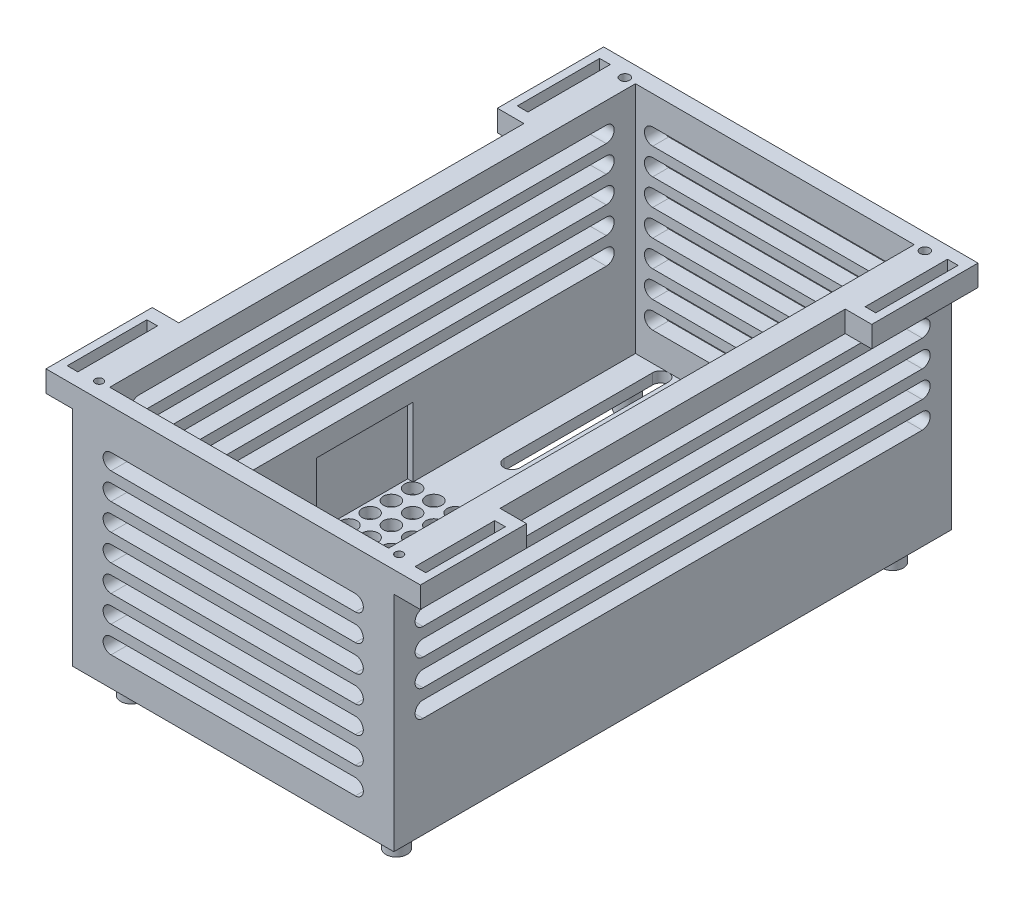
SolidWorks part; units mm, degrees
ref_plane "Front Plane" through (0, 0, 0) normal (0, 0, 1) x (1, 0, 0)
ref_plane "Top Plane" through (0, 0, 0) normal (0, 1, 0) x (1, 0, 0)
ref_plane "Right Plane" through (0, 0, 0) normal (1, 0, 0) x (0, 0, -1)
sketch "Sketch2" plane through (0, 0, 0) normal (0, 1, 0) x (1, 0, 0)
  line L1 (-30.25, 52.5) -> (30.25, 52.5)
  line L2 (-30.25, 52.5) -> (-30.25, -52.5)
  line L3 (-30.25, -52.5) -> (30.25, -52.5)
  line L4 (30.25, 52.5) -> (30.25, -52.5)
  line L5 (-30.25, 52.5) -> (30.25, -52.5) construction
  line L6 (-30.25, -52.5) -> (30.25, 52.5) construction
  point P0 (0, 0)
  dimension "D1" = 60.5
  dimension "D2" = 105
sketch "Sketch3" plane through (0, 0, 0) normal (0, 1, 0) x (1, 0, 0)
  line L0 (-30.25, -52.5) -> (30.25, -52.5) construction
  line L1 (30.25, 52.5) -> (26.25, 52.5)
  line L2 (30.25, 52.5) -> (30.25, -52.5)
  line L3 (30.25, -52.5) -> (26.25, -52.5)
  line L4 (26.25, 52.5) -> (26.25, -52.5)
  line L5 (0, 52.5) -> (0, -52.5) construction
  line L6 (-30.25, 52.5) -> (30.25, 52.5) construction
  line L7 (-30.25, -52.5) -> (-26.25, -52.5)
  line L8 (-26.25, 52.5) -> (-26.25, -52.5)
  line L9 (-30.25, 52.5) -> (-26.25, 52.5)
  line L10 (-30.25, 52.5) -> (-30.25, -52.5)
  line L12 (-30.25, 52.5) -> (30.25, 52.5)
  line L13 (-30.25, 52.5) -> (-30.25, 49.5)
  line L14 (-30.25, 49.5) -> (30.25, 49.5)
  line L15 (30.25, 52.5) -> (30.25, 49.5)
  dimension "D1" = 4
extrude "Boss-Extrude1" add sketch "Sketch3" along normal blind 46 contours L14 L10 L7 L8 | L5 L12 L8 L14 | L12 L5 L14 L4 | L14 L4 L3 L2 | L4 L14 L2 L1 | L10 L14 L8 L9
sketch "Sketch4" plane through (0, 0, 0) normal (0, 1, 0) x (1, 0, 0)
  line L1 (30.25, 52.5) -> (-30.25, 52.5)
  line L2 (30.25, 52.5) -> (30.25, -52.5)
  line L3 (30.25, -52.5) -> (-30.25, -52.5)
  line L4 (-30.25, 52.5) -> (-30.25, -52.5)
extrude "Boss-Extrude2" add sketch "Sketch4" along normal blind 2
sketch "Sketch5" plane through (0, 0, 0) normal (0, 1, 0) x (1, 0, 0)
  line L0 (0, -52.3325) -> (0, 52.2291) construction
  line L1 (30.25, -52.5) -> (30.25, -31.5) construction
  line L2 (30.25, 52.5) -> (30.25, -52.5) construction
  line L3 (30.25, -31.5) -> (-30.25, -31.5) construction
  line L4 (-30.25, 52.5) -> (-30.25, -52.5) construction
  line L5 (30.25, -28.023) -> (27.25, -28.023) construction
  line L7 (27.25, -31.5) -> (-13.75, -31.5)
  line L8 (27.25, -31.5) -> (27.25, 10.5)
  line L9 (27.25, 10.5) -> (-13.75, 10.5)
  line L10 (-13.75, -31.5) -> (-13.75, 10.5)
extrude "Cut-Extrude1" cut sketch "Sketch5" along normal blind 15
sketch "Sketch6" plane through (0, 0, 0) normal (0, 1, 0) x (1, 0, 0)
  circle A0 centre (-17.2261, -1.4891) radius 1.5
  circle A1 centre (-17.2261, -5.4891) radius 1.5
  circle A2 centre (-17.2261, -9.4891) radius 1.5
  circle A3 centre (-17.2261, 2.5109) radius 1.5
  circle A4 centre (-17.2261, 6.5109) radius 1.5
  circle A5 centre (-21.2261, -9.4891) radius 1.5
  circle A6 centre (-21.2261, -5.4891) radius 1.5
  circle A7 centre (-21.2261, -1.4891) radius 1.5
  circle A8 centre (-21.2261, 2.5109) radius 1.5
  circle A9 centre (-21.2261, 6.5109) radius 1.5
  circle A10 centre (-25.2261, -9.4891) radius 1.5
  circle A11 centre (-25.2261, -5.4891) radius 1.5
  circle A12 centre (-25.2261, -1.4891) radius 1.5
  circle A13 centre (-25.2261, 2.5109) radius 1.5
  circle A14 centre (-25.2261, 6.5109) radius 1.5
  dimension "D1" = 3
  dimension "D2" = 3
  dimension "D3" = 3
extrude "Cut-Extrude4" cut sketch "Sketch6" along normal blind 15
sketch "Sketch15" plane through (0, 0, 0) normal (0, -1, 0) x (1, 0, 0)
  line L0 (25.4448, -10.5) -> (25.4448, -15.5) construction
  line L1 (27.25, -10.5) -> (-13.75, -10.5) construction
  line L2 (25.4448, -15.5) -> (-17.3619, -15.5) construction
  line L3 (30.25, -15.5) -> (30.25, -52.5) construction
  line L4 (30.25, -52.5) -> (30.25, 52.5) construction
  line L5 (30.25, -52.5) -> (-30.25, -52.5) construction
  line L6 (0, -20) -> (0, -48) construction
  line L7 (5, -20) -> (5, -48) construction
  line L8 (1.5, -20) -> (1.5, -48)
  line L9 (-1.5, -20) -> (-1.5, -48)
  line L10 (6.5, -20) -> (6.5, -48)
  line L11 (3.5, -20) -> (3.5, -48)
  line L12 (10, -20) -> (10, -48) construction
  line L13 (11.5, -20) -> (11.5, -48)
  line L14 (8.5, -20) -> (8.5, -48)
  line L15 (15, -20) -> (15, -48) construction
  line L16 (16.5, -20) -> (16.5, -48)
  line L17 (13.5, -20) -> (13.5, -48)
  line L18 (20, -20) -> (20, -48) construction
  line L19 (21.5, -20) -> (21.5, -48)
  line L20 (18.5, -20) -> (18.5, -48)
  line L21 (-5, -20) -> (-5, -48) construction
  line L22 (-3.5, -20) -> (-3.5, -48)
  line L23 (-6.5, -20) -> (-6.5, -48)
  line L24 (-10, -20) -> (-10, -48) construction
  line L25 (-8.5, -20) -> (-8.5, -48)
  line L26 (-11.5, -20) -> (-11.5, -48)
  line L27 (-15, -20) -> (-15, -48) construction
  line L28 (-13.5, -20) -> (-13.5, -48)
  line L29 (-16.5, -20) -> (-16.5, -48)
  line L30 (-20, -20) -> (-20, -48) construction
  line L31 (-18.5, -20) -> (-18.5, -48)
  line L32 (-21.5, -20) -> (-21.5, -48)
  arc A0 (1.5, -20) -> (-1.5, -20) centre (0, -20) ccw
  arc A1 (-1.5, -48) -> (1.5, -48) centre (0, -48) ccw
  arc A2 (6.5, -20) -> (3.5, -20) centre (5, -20) ccw
  arc A3 (3.5, -48) -> (6.5, -48) centre (5, -48) ccw
  arc A4 (11.5, -20) -> (8.5, -20) centre (10, -20) ccw
  arc A5 (8.5, -48) -> (11.5, -48) centre (10, -48) ccw
  arc A6 (16.5, -20) -> (13.5, -20) centre (15, -20) ccw
  arc A7 (13.5, -48) -> (16.5, -48) centre (15, -48) ccw
  arc A8 (21.5, -20) -> (18.5, -20) centre (20, -20) ccw
  arc A9 (18.5, -48) -> (21.5, -48) centre (20, -48) ccw
  arc A10 (-3.5, -20) -> (-6.5, -20) centre (-5, -20) ccw
  arc A11 (-6.5, -48) -> (-3.5, -48) centre (-5, -48) ccw
  arc A12 (-8.5, -20) -> (-11.5, -20) centre (-10, -20) ccw
  arc A13 (-11.5, -48) -> (-8.5, -48) centre (-10, -48) ccw
  arc A14 (-13.5, -20) -> (-16.5, -20) centre (-15, -20) ccw
  arc A15 (-16.5, -48) -> (-13.5, -48) centre (-15, -48) ccw
  arc A16 (-18.5, -20) -> (-21.5, -20) centre (-20, -20) ccw
  arc A17 (-21.5, -48) -> (-18.5, -48) centre (-20, -48) ccw
  point P17 (0, -34)
  point P23 (5, -34)
  point P30 (10, -34)
  point P37 (15, -34)
  point P44 (20, -34)
  point P51 (-5, -34)
  point P58 (-10, -34)
  point P65 (-15, -34)
  point P72 (-20, -34)
  dimension "D1" = 5
  dimension "D2" = 5
extrude "Cut-Extrude15" cut sketch "Sketch15" against normal blind 15
sketch "Sketch16" plane through (-30.25, 0, 0) normal (-1, 0, 0) x (0, 0, 1)
  line L0 (-44, 40.488) -> (44, 40.488) construction
  line L1 (-44, 35.488) -> (44, 35.488) construction
  line L2 (-44, 41.988) -> (44, 41.988)
  line L3 (-44, 38.988) -> (44, 38.988)
  line L4 (-44, 36.988) -> (44, 36.988)
  line L5 (-44, 33.988) -> (44, 33.988)
  line L6 (-44, 30.488) -> (44, 30.488) construction
  line L7 (-44, 31.988) -> (44, 31.988)
  line L8 (-44, 28.988) -> (44, 28.988)
  line L9 (-44, 25.488) -> (44, 25.488) construction
  line L10 (-44, 26.988) -> (44, 26.988)
  line L11 (-44, 23.988) -> (44, 23.988)
  line L12 (-44, 20.488) -> (44, 20.488) construction
  line L13 (-44, 21.988) -> (44, 21.988)
  line L14 (-44, 18.988) -> (44, 18.988)
  arc A0 (-44, 41.988) -> (-44, 38.988) centre (-44, 40.488) ccw
  arc A1 (44, 38.988) -> (44, 41.988) centre (44, 40.488) ccw
  arc A2 (-44, 36.988) -> (-44, 33.988) centre (-44, 35.488) ccw
  arc A3 (44, 33.988) -> (44, 36.988) centre (44, 35.488) ccw
  arc A4 (-44, 31.988) -> (-44, 28.988) centre (-44, 30.488) ccw
  arc A5 (44, 28.988) -> (44, 31.988) centre (44, 30.488) ccw
  arc A6 (-44, 26.988) -> (-44, 23.988) centre (-44, 25.488) ccw
  arc A7 (44, 23.988) -> (44, 26.988) centre (44, 25.488) ccw
  arc A8 (-44, 21.988) -> (-44, 18.988) centre (-44, 20.488) ccw
  arc A9 (44, 18.988) -> (44, 21.988) centre (44, 20.488) ccw
  point P4 (0, 40.488)
  point P11 (0, 35.488)
  point P18 (0, 30.488)
  point P25 (0, 25.488)
  point P32 (0, 20.488)
  dimension "D1" = 5
extrude "Cut-Extrude16" cut sketch "Sketch16" against normal blind 15
sketch "Sketch20" plane through (30.25, 0, 0) normal (1, 0, 0) x (0, 0, -1)
  line L0 (0, 46) -> (0, 40.5) construction
  line L1 (52.5, 46) -> (-52.5, 46) construction
  line L2 (-47, 40.5) -> (47, 40.5) construction
  line L3 (-47, 35.5) -> (47, 35.5) construction
  line L4 (-47, 42) -> (47, 42)
  line L5 (-47, 39) -> (47, 39)
  line L6 (-47, 37) -> (47, 37)
  line L7 (-47, 34) -> (47, 34)
  line L8 (-47, 30.5) -> (47, 30.5) construction
  line L9 (-47, 32) -> (47, 32)
  line L10 (-47, 29) -> (47, 29)
  line L11 (-47, 25.5) -> (47, 25.5) construction
  line L12 (-47, 27) -> (47, 27)
  line L13 (-47, 24) -> (47, 24)
  line L14 (-47, 20.5) -> (47, 20.5) construction
  line L15 (-47, 22) -> (47, 22)
  line L16 (-47, 19) -> (47, 19)
  arc A0 (-47, 42) -> (-47, 39) centre (-47, 40.5) ccw
  arc A1 (47, 39) -> (47, 42) centre (47, 40.5) ccw
  arc A2 (-47, 37) -> (-47, 34) centre (-47, 35.5) ccw
  arc A3 (47, 34) -> (47, 37) centre (47, 35.5) ccw
  arc A4 (-47, 32) -> (-47, 29) centre (-47, 30.5) ccw
  arc A5 (47, 29) -> (47, 32) centre (47, 30.5) ccw
  arc A6 (-47, 27) -> (-47, 24) centre (-47, 25.5) ccw
  arc A7 (47, 24) -> (47, 27) centre (47, 25.5) ccw
  arc A8 (-47, 22) -> (-47, 19) centre (-47, 20.5) ccw
  arc A9 (47, 19) -> (47, 22) centre (47, 20.5) ccw
  point P9 (0, 40.5)
  point P16 (0, 35.5)
  point P23 (0, 30.5)
  point P30 (0, 25.5)
  point P37 (0, 20.5)
  dimension "D1" = 5
extrude "Cut-Extrude17" cut sketch "Sketch20" against normal blind 15
sketch "Sketch21" plane through (0, 0, -52.5) normal (0, 0, -1) x (-1, 0, 0)
  line L0 (0, 46) -> (0, 0) construction
  line L1 (30.25, 46) -> (-30.25, 46) construction
  line L2 (-30.25, 24) -> (30.25, 24) construction
  line L3 (30.25, 46) -> (30.25, 0) construction
  line L4 (-23, 24) -> (23, 24) construction
  line L5 (-23, 25.5647) -> (23, 25.5647)
  line L6 (-23, 22.4353) -> (23, 22.4353)
  line L7 (-23, 19) -> (23, 19) construction
  line L8 (-23, 20.5647) -> (23, 20.5647)
  line L9 (-23, 17.4353) -> (23, 17.4353)
  line L10 (-23, 14) -> (23, 14) construction
  line L11 (-23, 15.5647) -> (23, 15.5647)
  line L12 (-23, 12.4353) -> (23, 12.4353)
  line L13 (-23, 9) -> (23, 9) construction
  line L14 (-23, 10.5647) -> (23, 10.5647)
  line L15 (-23, 7.4353) -> (23, 7.4353)
  line L16 (-23, 29) -> (23, 29) construction
  line L17 (-23, 30.5647) -> (23, 30.5647)
  line L18 (-23, 27.4353) -> (23, 27.4353)
  line L19 (-23, 34) -> (23, 34) construction
  line L20 (-23, 35.5647) -> (23, 35.5647)
  line L21 (-23, 32.4353) -> (23, 32.4353)
  line L22 (-23, 39) -> (23, 39) construction
  line L23 (-23, 40.5647) -> (23, 40.5647)
  line L24 (-23, 37.4353) -> (23, 37.4353)
  arc A0 (-23, 25.5647) -> (-23, 22.4353) centre (-23, 24) ccw
  arc A1 (23, 22.4353) -> (23, 25.5647) centre (23, 24) ccw
  arc A2 (-23, 20.5647) -> (-23, 17.4353) centre (-23, 19) ccw
  arc A3 (23, 17.4353) -> (23, 20.5647) centre (23, 19) ccw
  arc A4 (-23, 15.5647) -> (-23, 12.4353) centre (-23, 14) ccw
  arc A5 (23, 12.4353) -> (23, 15.5647) centre (23, 14) ccw
  arc A6 (-23, 10.5647) -> (-23, 7.4353) centre (-23, 9) ccw
  arc A7 (23, 7.4353) -> (23, 10.5647) centre (23, 9) ccw
  arc A8 (-23, 30.5647) -> (-23, 27.4353) centre (-23, 29) ccw
  arc A9 (23, 27.4353) -> (23, 30.5647) centre (23, 29) ccw
  arc A10 (-23, 35.5647) -> (-23, 32.4353) centre (-23, 34) ccw
  arc A11 (23, 32.4353) -> (23, 35.5647) centre (23, 34) ccw
  arc A12 (-23, 40.5647) -> (-23, 37.4353) centre (-23, 39) ccw
  arc A13 (23, 37.4353) -> (23, 40.5647) centre (23, 39) ccw
  point P12 (0, 24)
  point P20 (0, 19)
  point P27 (0, 14)
  point P34 (0, 9)
  point P41 (0, 29)
  point P48 (0, 34)
  point P55 (0, 39)
  dimension "D1" = 4
  dimension "D2" = 4
extrude "Cut-Extrude20" cut sketch "Sketch21" against normal blind 15
sketch "Sketch22" plane through (0, 0, 52.5) normal (0, 0, 1) x (1, 0, 0)
  line L1 (-30.25, 46) -> (30.25, 46)
  line L2 (-30.25, 46) -> (-30.25, 0)
  line L3 (-30.25, 0) -> (30.25, 0)
  line L4 (30.25, 46) -> (30.25, 0)
extrude "Boss-Extrude3" add sketch "Sketch22" against normal blind 3
sketch "Sketch24" plane through (0, 0, 52.5) normal (0, 0, 1) x (1, 0, 0)
  line L0 (0, 46) -> (0, 0) construction
  line L1 (30.25, 46) -> (-30.25, 46) construction
  line L2 (-30.25, 21.988) -> (30.25, 21.988) construction
  line L3 (30.25, 46) -> (30.25, 0) construction
  line L4 (-23, 21.988) -> (23, 21.988) construction
  line L5 (-23, 16.988) -> (23, 16.988) construction
  line L6 (-23, 23.488) -> (23, 23.488)
  line L7 (-23, 20.488) -> (23, 20.488)
  line L8 (-23, 18.488) -> (23, 18.488)
  line L9 (-23, 15.488) -> (23, 15.488)
  line L10 (-23, 11.988) -> (23, 11.988) construction
  line L11 (-23, 13.488) -> (23, 13.488)
  line L12 (-23, 10.488) -> (23, 10.488)
  line L13 (-23, 6.988) -> (23, 6.988) construction
  line L14 (-23, 8.488) -> (23, 8.488)
  line L15 (-23, 5.488) -> (23, 5.488)
  line L16 (-23, 26.988) -> (23, 26.988) construction
  line L17 (-23, 28.488) -> (23, 28.488)
  line L18 (-23, 25.488) -> (23, 25.488)
  line L19 (-23, 31.988) -> (23, 31.988) construction
  line L20 (-23, 33.488) -> (23, 33.488)
  line L21 (-23, 30.488) -> (23, 30.488)
  line L22 (-23, 36.988) -> (23, 36.988) construction
  line L23 (-23, 38.488) -> (23, 38.488)
  line L24 (-23, 35.488) -> (23, 35.488)
  arc A0 (-23, 23.488) -> (-23, 20.488) centre (-23, 21.988) ccw
  arc A1 (23, 20.488) -> (23, 23.488) centre (23, 21.988) ccw
  arc A2 (-23, 18.488) -> (-23, 15.488) centre (-23, 16.988) ccw
  arc A3 (23, 15.488) -> (23, 18.488) centre (23, 16.988) ccw
  arc A4 (-23, 13.488) -> (-23, 10.488) centre (-23, 11.988) ccw
  arc A5 (23, 10.488) -> (23, 13.488) centre (23, 11.988) ccw
  arc A6 (-23, 8.488) -> (-23, 5.488) centre (-23, 6.988) ccw
  arc A7 (23, 5.488) -> (23, 8.488) centre (23, 6.988) ccw
  arc A8 (-23, 28.488) -> (-23, 25.488) centre (-23, 26.988) ccw
  arc A9 (23, 25.488) -> (23, 28.488) centre (23, 26.988) ccw
  arc A10 (-23, 33.488) -> (-23, 30.488) centre (-23, 31.988) ccw
  arc A11 (23, 30.488) -> (23, 33.488) centre (23, 31.988) ccw
  arc A12 (-23, 38.488) -> (-23, 35.488) centre (-23, 36.988) ccw
  arc A13 (23, 35.488) -> (23, 38.488) centre (23, 36.988) ccw
  point P14 (0, 21.988)
  point P20 (0, 16.988)
  point P27 (0, 11.988)
  point P34 (0, 6.988)
  point P41 (0, 26.988)
  point P48 (0, 31.988)
  point P55 (0, 36.988)
  dimension "D1" = 4
  dimension "D2" = 4
extrude "Cut-Extrude21" cut sketch "Sketch24" against normal blind 23
sketch "Sketch26" plane through (0, 46, 0) normal (0, 1, 0) x (1, 0, 0)
  line L0 (26.25, 49.5) -> (30.25, 49.5) construction
  line L1 (30.25, 52.5) -> (30.25, -52.5) construction
  line L2 (0, 52.5) -> (0, 44.958) construction
  line L3 (-30.25, 52.5) -> (30.25, 52.5) construction
  circle A0 centre (28.25, 49.5) radius 0.9
  circle A1 centre (-28.25, 49.5) radius 0.9
extrude "Cut-Extrude22" cut sketch "Sketch26" against normal blind 4
sketch "Sketch27" plane through (0, 46, 0) normal (0, 1, 0) x (1, 0, 0)
  line L0 (26.25, -49.5) -> (30.25, -49.5) construction
  line L1 (30.25, 52.5) -> (30.25, -52.5) construction
  line L2 (0, -49.5) -> (0, -43.1302) construction
  line L3 (26.25, -49.5) -> (-26.25, -49.5) construction
  circle A0 centre (28.25, -49.5) radius 0.75
  circle A1 centre (-28.25, -49.5) radius 0.75
extrude "Cut-Extrude23" cut sketch "Sketch27" against normal blind 4
sketch "Sketch29" plane through (-26.25, 0, 0) normal (1, 0, 0) x (0, 0, -1)
  line L1 (-10.5854, 2) -> (7.6071, 2)
  line L2 (-10.5854, 2) -> (-10.5854, 15)
  line L3 (-10.5854, 15) -> (7.6071, 15)
  line L4 (7.6071, 2) -> (7.6071, 15)
extrude "Cut-Extrude24" cut sketch "Sketch29" against normal blind 1
sketch "Sketch32" plane through (-30.25, 0, 0) normal (-1, 0, 0) x (0, 0, 1)
  line L0 (-52.5, 0) -> (52.5, 0) construction
  line L1 (52.5, 23) -> (-52.5, 23) construction
  line L2 (52.5, 46) -> (52.5, 0) construction
  line L3 (-52.5, 46) -> (-52.5, 0) construction
sketch "Sketch38" plane through (-30.25, 0, 0) normal (-1, 0, 0) x (0, 0, 1)
  line L0 (44, 41.988) -> (-44, 41.988) construction
  line L1 (-52.5, 46) -> (-32.5, 46)
  line L2 (-52.5, 46) -> (-52.5, 41.988)
  line L3 (-52.5, 41.988) -> (-32.5, 41.988)
  line L4 (-32.5, 46) -> (-32.5, 41.988)
  line L6 (52.5, 46) -> (32.5, 46)
  line L7 (52.5, 46) -> (52.5, 41.988)
  line L8 (52.5, 41.988) -> (32.5, 41.988)
  line L9 (32.5, 46) -> (32.5, 41.988)
  dimension "D1" = 20
  dimension "D2" = 20
extrude "Boss-Extrude10" add sketch "Sketch38" along normal blind 5
sketch "Sketch39" plane through (30.25, 0, 0) normal (1, 0, 0) x (0, 0, -1)
  line L0 (47, 42) -> (-47, 42) construction
  line L1 (-52.5, 46) -> (-32.5, 46)
  line L2 (-52.5, 46) -> (-52.5, 42)
  line L3 (-52.5, 42) -> (-32.5, 42)
  line L4 (-32.5, 46) -> (-32.5, 42)
  line L6 (52.5, 46) -> (32.5, 46)
  line L7 (52.5, 46) -> (52.5, 42)
  line L8 (52.5, 42) -> (32.5, 42)
  line L9 (32.5, 46) -> (32.5, 42)
  dimension "D1" = 20
  dimension "D2" = 20
extrude "Boss-Extrude11" add sketch "Sketch39" along normal blind 5
sketch "Sketch41" plane through (0, 46, 0) normal (0, 1, 0) x (1, 0, 0)
  line L0 (-32.75, -32.5) -> (-32.75, -52.5) construction
  line L1 (-35.25, -32.5) -> (-30.25, -32.5) construction
  line L2 (35.25, -52.5) -> (-35.25, -52.5) construction
  line L3 (-35.25, -42.5) -> (-30.25, -42.5) construction
  line L4 (-35.25, -52.5) -> (-35.25, -32.5) construction
  line L5 (-30.25, 52.5) -> (-30.25, -52.5) construction
  line L6 (0, -49.5) -> (0, -40.7214) construction
  line L7 (-33.75, -50) -> (-31.75, -50)
  line L8 (-33.75, -50) -> (-33.75, -35)
  line L9 (-33.75, -35) -> (-31.75, -35)
  line L10 (-31.75, -50) -> (-31.75, -35)
  line L11 (-33.75, -50) -> (-31.75, -35) construction
  line L12 (-33.75, -35) -> (-31.75, -50) construction
  line L13 (26.25, -49.5) -> (-26.25, -49.5) construction
  line L14 (33.75, -35) -> (31.75, -35)
  line L15 (31.75, -50) -> (31.75, -35)
  line L16 (33.75, -50) -> (31.75, -50)
  line L17 (33.75, -50) -> (33.75, -35)
  point P12 (-32.75, -42.5)
extrude "Cut-Extrude25" cut sketch "Sketch41" against normal blind 5
sketch "Sketch42" plane through (0, 46, 0) normal (0, 1, 0) x (1, 0, 0)
  line L0 (-35.25, 52.5) -> (-30.25, 52.5) construction
  line L1 (-32.75, 52.5) -> (-32.75, 32.5) construction
  line L2 (-35.25, 32.5) -> (-30.25, 32.5) construction
  line L3 (-35.25, 42.5) -> (-30.25, 42.5) construction
  line L4 (-35.25, 32.5) -> (-35.25, 52.5) construction
  line L5 (-30.25, 52.5) -> (-30.25, -52.5) construction
  line L6 (0, 52.5) -> (0, 36.1604) construction
  line L7 (-33.75, 34.75) -> (-31.75, 34.75)
  line L8 (-33.75, 34.75) -> (-33.75, 50.25)
  line L9 (-33.75, 50.25) -> (-31.75, 50.25)
  line L10 (-31.75, 34.75) -> (-31.75, 50.25)
  line L11 (-33.75, 34.75) -> (-31.75, 50.25) construction
  line L12 (-33.75, 50.25) -> (-31.75, 34.75) construction
  line L13 (-30.25, 52.5) -> (30.25, 52.5) construction
  line L14 (33.75, 50.25) -> (31.75, 50.25)
  line L15 (31.75, 34.75) -> (31.75, 50.25)
  line L16 (33.75, 34.75) -> (31.75, 34.75)
  line L17 (33.75, 34.75) -> (33.75, 50.25)
  point P14 (-32.75, 42.5)
extrude "Cut-Extrude26" cut sketch "Sketch42" against normal blind 5
sketch "Sketch43" plane through (0, 0, 0) normal (0, -1, 0) x (1, 0, 0)
  line L0 (-30.1253, 0) -> (30.1581, 0) construction
  line L1 (0, 52.4106) -> (0, 44.1401) construction
  circle A0 centre (-24.9588, 46.7191) radius 2
  circle A1 centre (24.9588, 46.7191) radius 2
  circle A2 centre (24.9588, -46.7191) radius 2
  circle A3 centre (-24.9588, -46.7191) radius 2
extrude "Boss-Extrude13" add sketch "Sketch43" along normal blind 5
